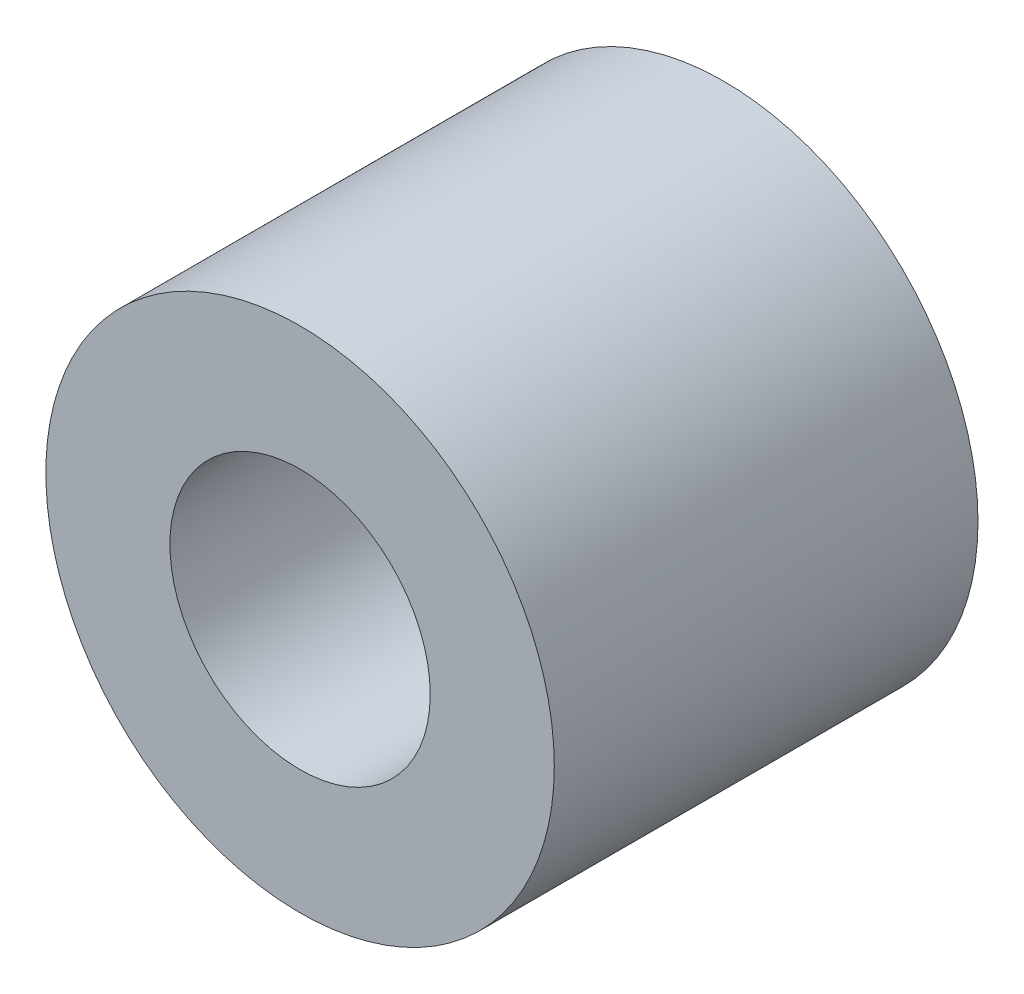
SolidWorks part; units mm, degrees
material "Nylon 101"
ref_plane "Front Plane" through (0, 0, 0) normal (0, 0, 1) x (1, 0, 0)
ref_plane "Top Plane" through (0, 0, 0) normal (0, 1, 0) x (1, 0, 0)
ref_plane "Right Plane" through (0, 0, 0) normal (1, 0, 0) x (0, 0, -1)
sketch "Sketch1" plane through (0, 0, 0) normal (0, 0, 1) x (1, 0, 0)
  line L0 (0, 2.4384) -> (0, 4.7625) construction
  line L1 (0, -2.4384) -> (0, -4.7625) construction
  circle A0 centre (0, 0) radius 4.7625
  circle A1 centre (0, 0) radius 2.4384
  dimension "OD" = 9.525
  dimension "ID" = 4.8768
sketch "Sketch2" plane through (0, 0, 0) normal (1, 0, 0) x (0, 0, -1)
  line L0 (-3.9688, 2.4384) -> (3.9688, 2.4384) construction
  line L1 (-3.9688, -2.4384) -> (3.9688, -2.4384) construction
  line L2 (-3.9688, -4.7625) -> (3.9688, -4.7625) construction
  line L3 (-3.9688, 4.7625) -> (3.9688, 4.7625) construction
  dimension "Length" = 7.9375
extrude "Extrude1" add sketch "Sketch1" along normal up to vertex (3.9688 mm away) and the other way up to vertex (3.9688 mm away) up to point (0, 2.4384, 3.9688) other way up to point (0, 2.4384, -3.9688)
sketch "Sketch3" plane through (0, 0, 3.9688) normal (0, 0, 1) x (1, 0, 0)
  circle A0 centre (0, 0) radius 2.4384 construction
  circle A3 centre (0, 0) radius 2.4384
  point P3 (-2.4384, 0)
